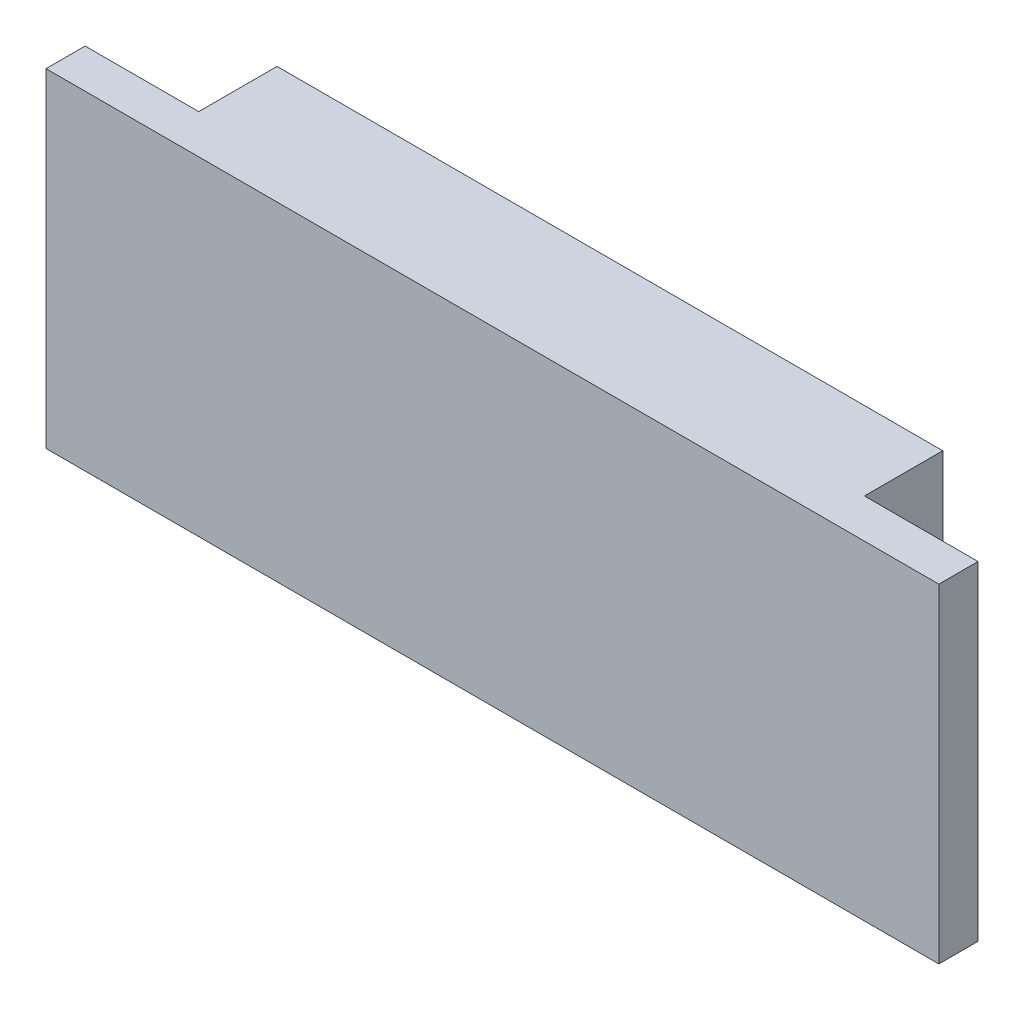
SolidWorks part; units mm, degrees
material "ABS"
ref_plane "Plan de face" through (0, 0, 0) normal (0, 0, 1) x (1, 0, 0)
ref_plane "Plan de dessus" through (0, 0, 0) normal (0, 1, 0) x (1, 0, 0)
ref_plane "Plan de droite" through (0, 0, 0) normal (1, 0, 0) x (0, 0, -1)
sketch "Sketch1" plane through (0, 0, 0) normal (0, 0, 1) x (1, 0, 0)
  line L1 (-28.5, -10.5) -> (28.5, -10.5)
  line L2 (-28.5, -10.5) -> (-28.5, 10.5)
  line L3 (-28.5, 10.5) -> (28.5, 10.5)
  line L4 (28.5, -10.5) -> (28.5, 10.5)
  line L5 (-28.5, -10.5) -> (28.5, 10.5) construction
  line L6 (-28.5, 10.5) -> (28.5, -10.5) construction
  point P0 (0, 0)
  dimension "D1" = 57
  dimension "D2" = 21
extrude "Boss-Extrude1" add sketch "Sketch1" along normal blind 2.5
sketch "Sketch2" plane through (0, 0, 0) normal (0, 0, -1) x (-1, 0, 0)
  line L0 (-28.5, 10.5) -> (28.5, 10.5) construction
  line L1 (-21.25, -10.5) -> (21.25, -10.5)
  line L2 (-21.25, -10.5) -> (-21.25, 10.5)
  line L3 (-21.25, 10.5) -> (21.25, 10.5)
  line L4 (21.25, -10.5) -> (21.25, 10.5)
  line L5 (-21.25, -10.5) -> (21.25, 10.5) construction
  line L6 (-21.25, 10.5) -> (21.25, -10.5) construction
  point P0 (0, 0)
  dimension "D1" = 42.5
extrude "Boss-Extrude2" add sketch "Sketch2" along normal blind 5
